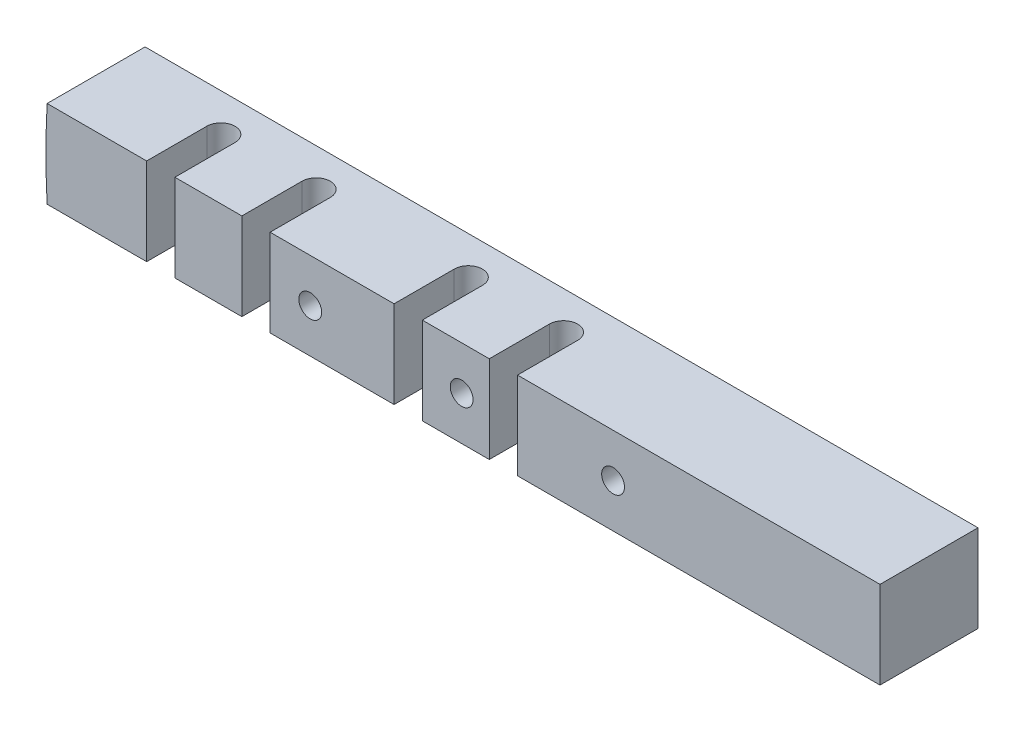
SolidWorks part; units mm, degrees
ref_plane "Front Plane" through (0, 0, 0) normal (0, 0, 1) x (1, 0, 0)
ref_plane "Top Plane" through (0, 0, 0) normal (0, 1, 0) x (1, 0, 0)
ref_plane "Right Plane" through (0, 0, 0) normal (1, 0, 0) x (0, 0, -1)
sketch "Sketch2" plane through (0, 0, 0) normal (0, 0, 1) x (1, 0, 0)
  line L0 (0, 0) -> (-166.8477, 0) construction
  line L1 (7.4981, 4.318) -> (-75.8231, 4.318)
  line L2 (7.4981, 4.318) -> (7.4981, -4.318)
  line L3 (7.4981, -4.318) -> (-75.8231, -4.318)
  arc A0 (-75.8231, -4.318) -> (-75.8231, 4.318) centre (0, 0) cw
  point P5 (-75.946, 0)
  point P9 (7.4981, 0)
  dimension "D1" = 75.946
  dimension "D2" = 83.4441
  dimension "D3" = 4.318
extrude "Boss-Extrude2" add sketch "Sketch2" along normal blind 13.97
sketch "Sketch3" plane through (0, -4.318, 0) normal (0, -1, 0) x (-1, 0, 0)
  line L0 (63.1774, -10.2235) -> (63.1774, -3.7465)
  line L1 (29.2684, -19.438) -> (29.2684, 16.2707) construction
  line L2 (-7.4981, -13.97) -> (-7.4981, 0) construction
  line L3 (29.2684, -10.2235) -> (29.2684, -3.7465)
  line L4 (32.0624, -10.2235) -> (32.0624, -3.7465)
  line L5 (29.2684, -3.7465) -> (32.0624, -3.7465) construction
  line L6 (30.6654, -3.7465) -> (30.6654, -19.438) construction
  line L7 (35.3771, -21.5467) -> (35.3771, 8.2742) construction
  line L8 (38.6918, -10.2235) -> (38.6918, -3.7465)
  line L9 (41.4858, -10.2235) -> (41.4858, -3.7465)
  line L10 (47.6199, -19.438) -> (47.6199, 16.2707) construction
  line L11 (65.9714, -10.2235) -> (65.9714, -3.7465)
  line L12 (53.754, -10.2235) -> (53.754, -3.7465)
  line L13 (56.548, -10.2235) -> (56.548, -3.7465)
  line L14 (75.8231, -6.985) -> (-17.4467, -6.985) construction
  line L15 (75.8231, -13.97) -> (75.8231, 0) construction
  arc A0 (32.0624, -3.7465) -> (29.2684, -3.7465) centre (30.6654, -3.7465) ccw
  arc A1 (29.2684, -10.2235) -> (32.0624, -10.2235) centre (30.6654, -10.2235) ccw
  arc A2 (38.6918, -3.7465) -> (41.4858, -3.7465) centre (40.0888, -3.7465) cw
  arc A3 (41.4858, -10.2235) -> (38.6918, -10.2235) centre (40.0888, -10.2235) cw
  arc A4 (63.1774, -3.7465) -> (65.9714, -3.7465) centre (64.5744, -3.7465) cw
  arc A5 (65.9714, -10.2235) -> (63.1774, -10.2235) centre (64.5744, -10.2235) cw
  arc A6 (56.548, -3.7465) -> (53.754, -3.7465) centre (55.151, -3.7465) ccw
  arc A7 (53.754, -10.2235) -> (56.548, -10.2235) centre (55.151, -10.2235) ccw
  point P37 (32.0624, -6.985)
  dimension "D6" = 1.397
  dimension "D1" = 36.7665
  dimension "D2" = 2.794
  dimension "D3" = 6.1087
  dimension "D4" = 18.3515
  dimension "D5" = 6.477
extrude "Cut-Extrude1" cut sketch "Sketch3" against normal through all
sketch "Sketch4" plane through (0, -4.318, 0) normal (0, -1, 0) x (1, 0, 0)
  line L0 (-75.8231, 13.97) -> (7.4981, 13.97) construction
  line L2 (7.4981, 13.97) -> (6.604, 13.97)
  line L3 (7.4981, 13.97) -> (7.4981, -0.8389)
  line L4 (7.4981, -0.8389) -> (6.604, -0.8389)
  line L5 (6.604, 13.97) -> (6.604, -0.8389)
  point P0 (-75.946, 13.97)
  point P1 (6.604, 13.97)
  dimension "D1" = 82.55
extrude "Cut-Extrude2" cut sketch "Sketch4" against normal through all
sketch "Sketch5" plane through (0, -4.318, 0) normal (0, -1, 0) x (1, 0, 0)
  line L1 (-87.3381, 16.3679) -> (23.0308, 16.3679)
  line L2 (-87.3381, 16.3679) -> (-87.3381, 9.6975)
  line L3 (-87.3381, 9.6975) -> (23.0308, 9.6975)
  line L4 (23.0308, 16.3679) -> (23.0308, 9.6975)
extrude "Cut-Extrude3" cut sketch "Sketch5" against normal through all
sketch "Sketch6" plane through (0, 0, 9.6975) normal (0, 0, 1) x (1, 0, 0)
  arc A0 (-75.8231, 4.318) -> (-75.8231, -4.318) centre (0, 0) ccw construction
  circle A1 centre (-49.784, 0) radius 1.1303
  circle A2 centre (-34.798, 0) radius 1.1303
  circle A3 centre (-19.812, 0) radius 1.1303
  point P0 (-75.946, 0)
  dimension "D2" = 2.2606
  dimension "D1" = 26.162
  dimension "D3" = 3
extrude "Cut-Extrude4" cut sketch "Sketch6" against normal blind 5.08
